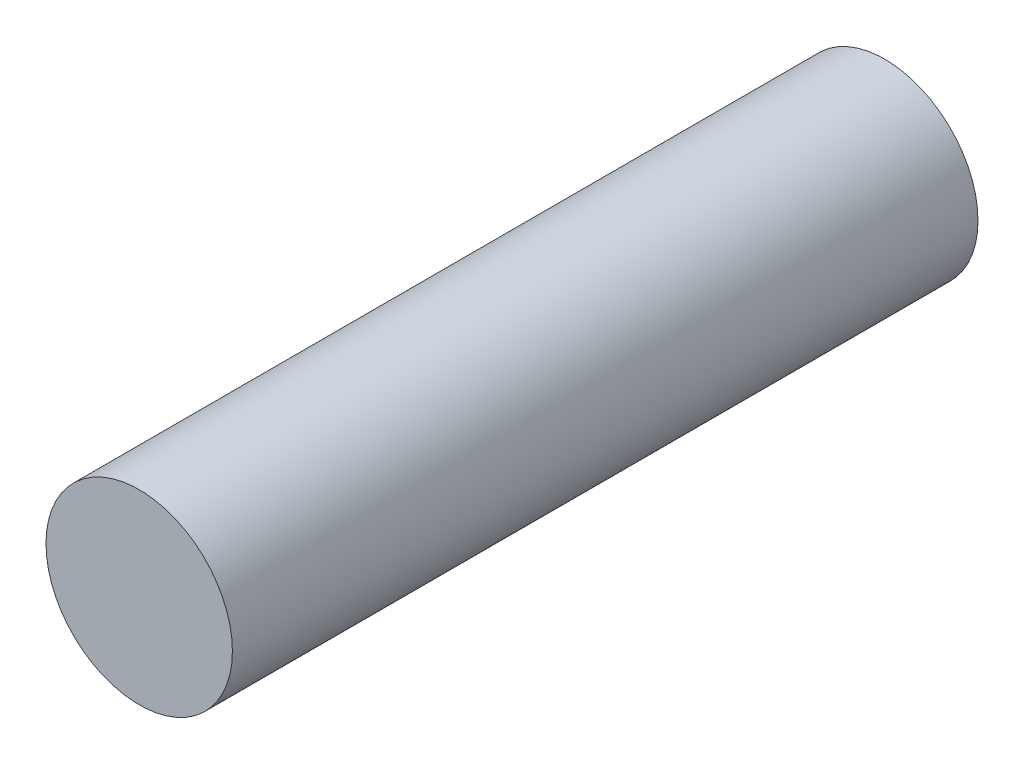
SolidWorks part; units mm, degrees
ref_plane "前视基准面" through (0, 0, 0) normal (0, 0, 1) x (1, 0, 0)
ref_plane "上视基准面" through (0, 0, 0) normal (0, 1, 0) x (1, 0, 0)
ref_plane "右视基准面" through (0, 0, 0) normal (1, 0, 0) x (0, 0, -1)
sketch "草图1" plane through (0, 0, 0) normal (0, 0, 1) x (1, 0, 0)
  circle A0 centre (0, 0) radius 1.5
  dimension "D1" = 3
extrude "凸台-拉伸1" add sketch "草图1" along normal blind 12
